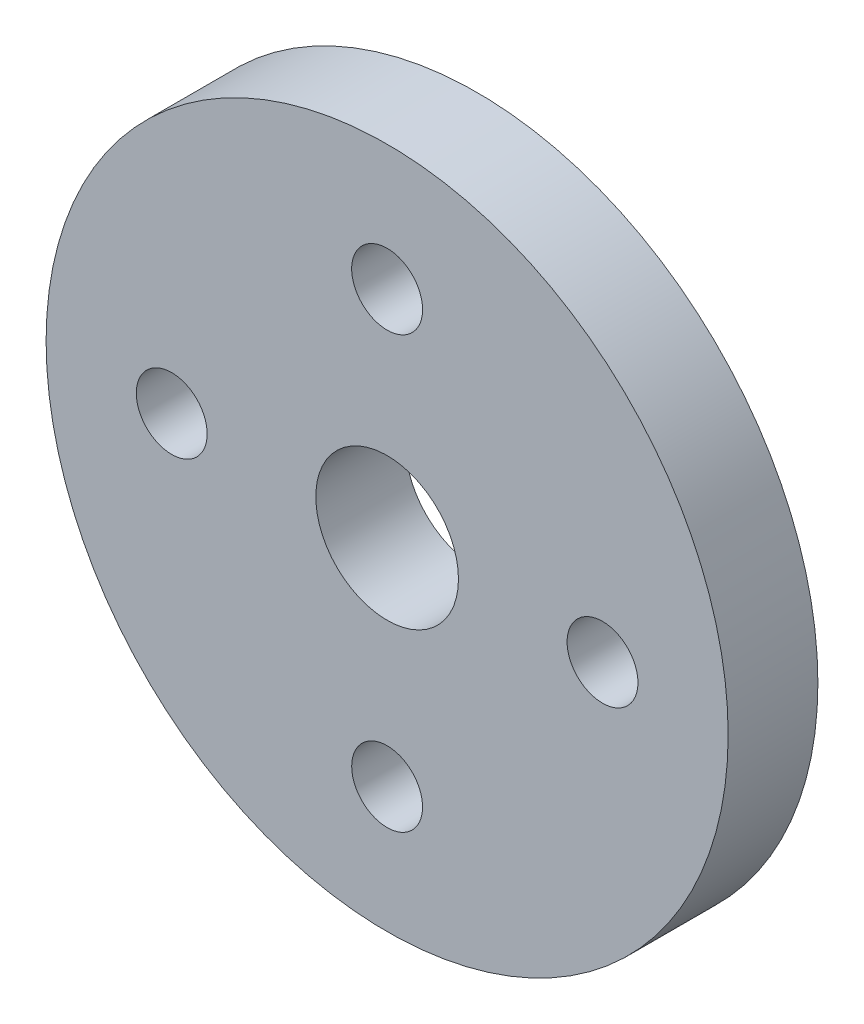
SolidWorks part; units mm, degrees
ref_plane "Front Plane" through (0, 0, 0) normal (0, 0, 1) x (1, 0, 0)
ref_plane "Top Plane" through (0, 0, 0) normal (0, 1, 0) x (1, 0, 0)
ref_plane "Right Plane" through (0, 0, 0) normal (1, 0, 0) x (0, 0, -1)
sketch "Sketch1" plane through (0, 0, 0) normal (0, 0, 1) x (1, 0, 0)
  line L0 (0, 0) -> (0, 25.6249) construction
  line L1 (0, 0) -> (25.5986, 0) construction
  circle A0 centre (0, 0) radius 19
  circle A1 centre (0, 12) radius 1.975
  circle A2 centre (0, -12) radius 1.975
  circle A3 centre (12, 0) radius 1.975
  circle A4 centre (-12, 0) radius 1.975
  circle A5 centre (0, 0) radius 3.975
  dimension "D1" = 38
  dimension "D2" = 3.95
  dimension "D4" = 3.95
  dimension "D6" = 7.95
  dimension "D3" = 12
  dimension "D5" = 12
extrude "Boss-Extrude1" add sketch "Sketch1" along normal blind 5
